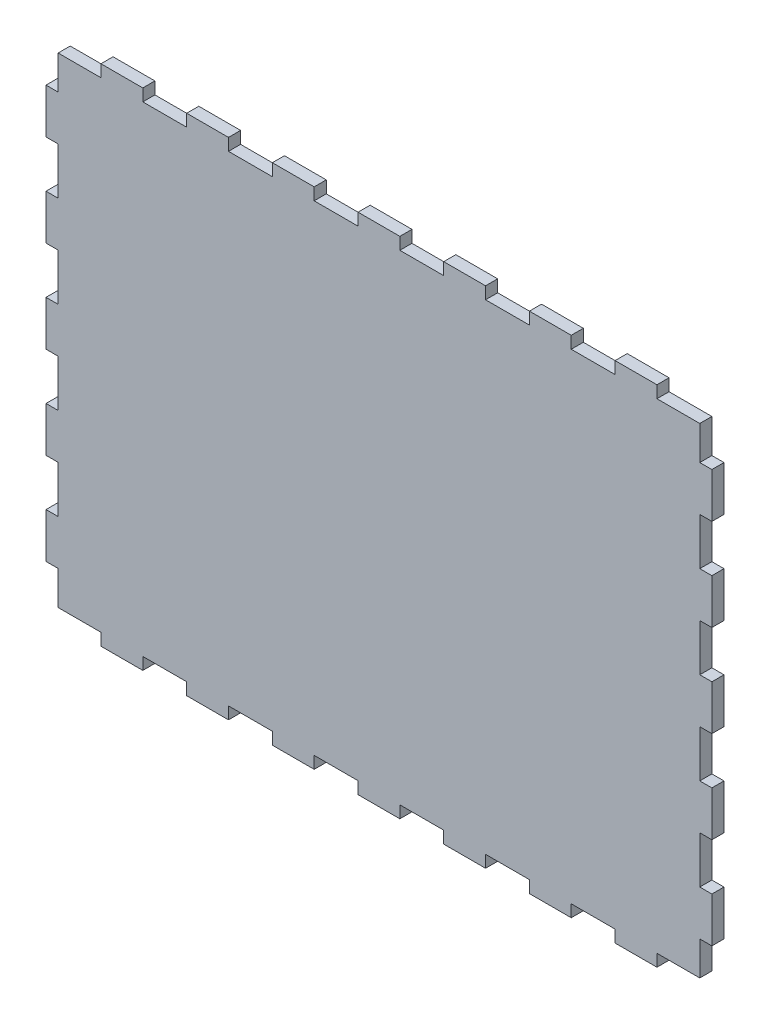
SolidWorks part; units mm, degrees
material "Plywood"
ref_plane "Front Plane" through (0, 0, 0) normal (0, 0, 1) x (1, 0, 0)
ref_plane "Top Plane" through (0, 0, 0) normal (0, 1, 0) x (1, 0, 0)
ref_plane "Right Plane" through (0, 0, 0) normal (1, 0, 0) x (0, 0, -1)
ref_plane "Plane1" through (0, 0, 6) normal (0, 0, 1) x (1, 0, 0)
sketch "Sketch1" plane through (0, 0, 6) normal (0, 0, 1) x (1, 0, 0)
  line L0 (302.7667, 244) -> (302.7667, 250)
  line L1 (302.7667, 250) -> (282.0333, 250)
  line L2 (282.0333, 250) -> (282.0333, 244)
  line L3 (282.0333, 244) -> (260.3, 244)
  line L4 (260.3, 244) -> (260.3, 250)
  line L5 (260.3, 250) -> (239.5667, 250)
  line L6 (239.5667, 250) -> (239.5667, 244)
  line L7 (239.5667, 244) -> (217.8333, 244)
  line L8 (217.8333, 244) -> (217.8333, 250)
  line L9 (217.8333, 250) -> (197.1, 250)
  line L10 (197.1, 250) -> (197.1, 244)
  line L11 (197.1, 244) -> (175.3667, 244)
  line L12 (175.3667, 244) -> (175.3667, 250)
  line L13 (175.3667, 250) -> (154.6333, 250)
  line L14 (154.6333, 250) -> (154.6333, 244)
  line L15 (154.6333, 244) -> (132.9, 244)
  line L16 (132.9, 244) -> (132.9, 250)
  line L17 (132.9, 250) -> (112.1667, 250)
  line L18 (112.1667, 250) -> (112.1667, 244)
  line L19 (112.1667, 244) -> (90.4333, 244)
  line L20 (90.4333, 244) -> (90.4333, 250)
  line L21 (90.4333, 250) -> (69.7, 250)
  line L22 (69.7, 250) -> (69.7, 244)
  line L23 (69.7, 244) -> (47.9667, 244)
  line L24 (47.9667, 244) -> (47.9667, 250)
  line L25 (47.9667, 250) -> (27.2333, 250)
  line L26 (27.2333, 250) -> (27.2333, 244)
  line L27 (27.2333, 244) -> (6, 244)
  line L28 (6, 244) -> (6, 227.2273)
  line L29 (6, 227.2273) -> (0, 227.2273)
  line L30 (0, 227.2273) -> (0, 204.9545)
  line L31 (0, 204.9545) -> (6, 204.9545)
  line L32 (6, 204.9545) -> (6, 181.6818)
  line L33 (6, 181.6818) -> (0, 181.6818)
  line L34 (0, 181.6818) -> (0, 159.4091)
  line L35 (0, 159.4091) -> (6, 159.4091)
  line L36 (6, 159.4091) -> (6, 136.1364)
  line L37 (6, 136.1364) -> (0, 136.1364)
  line L38 (0, 136.1364) -> (0, 113.8636)
  line L39 (0, 113.8636) -> (6, 113.8636)
  line L40 (6, 113.8636) -> (6, 90.5909)
  line L41 (6, 90.5909) -> (0, 90.5909)
  line L42 (0, 90.5909) -> (0, 68.3182)
  line L43 (0, 68.3182) -> (6, 68.3182)
  line L44 (6, 68.3182) -> (6, 45.0455)
  line L45 (6, 45.0455) -> (0, 45.0455)
  line L46 (0, 45.0455) -> (0, 22.7727)
  line L47 (0, 22.7727) -> (6, 22.7727)
  line L48 (6, 22.7727) -> (6, 6)
  line L49 (6, 6) -> (27.2333, 6)
  line L50 (27.2333, 6) -> (27.2333, 0)
  line L51 (27.2333, 0) -> (47.9667, 0)
  line L52 (47.9667, 0) -> (47.9667, 6)
  line L53 (47.9667, 6) -> (69.7, 6)
  line L54 (69.7, 6) -> (69.7, 0)
  line L55 (69.7, 0) -> (90.4333, 0)
  line L56 (90.4333, 0) -> (90.4333, 6)
  line L57 (90.4333, 6) -> (112.1667, 6)
  line L58 (112.1667, 6) -> (112.1667, 0)
  line L59 (112.1667, 0) -> (132.9, 0)
  line L60 (132.9, 0) -> (132.9, 6)
  line L61 (132.9, 6) -> (154.6333, 6)
  line L62 (154.6333, 6) -> (154.6333, 0)
  line L63 (154.6333, 0) -> (175.3667, 0)
  line L64 (175.3667, 0) -> (175.3667, 6)
  line L65 (175.3667, 6) -> (197.1, 6)
  line L66 (197.1, 6) -> (197.1, 0)
  line L67 (197.1, 0) -> (217.8333, 0)
  line L68 (217.8333, 0) -> (217.8333, 6)
  line L69 (217.8333, 6) -> (239.5667, 6)
  line L70 (239.5667, 6) -> (239.5667, 0)
  line L71 (239.5667, 0) -> (260.3, 0)
  line L72 (260.3, 0) -> (260.3, 6)
  line L73 (260.3, 6) -> (282.0333, 6)
  line L74 (282.0333, 6) -> (282.0333, 0)
  line L75 (282.0333, 0) -> (302.7667, 0)
  line L76 (302.7667, 0) -> (302.7667, 6)
  line L77 (302.7667, 6) -> (324, 6)
  line L78 (324, 6) -> (324, 22.7727)
  line L79 (324, 22.7727) -> (330, 22.7727)
  line L80 (330, 22.7727) -> (330, 45.0455)
  line L81 (330, 45.0455) -> (324, 45.0455)
  line L82 (324, 45.0455) -> (324, 68.3182)
  line L83 (324, 68.3182) -> (330, 68.3182)
  line L84 (330, 68.3182) -> (330, 90.5909)
  line L85 (330, 90.5909) -> (324, 90.5909)
  line L86 (324, 90.5909) -> (324, 113.8636)
  line L87 (324, 113.8636) -> (330, 113.8636)
  line L88 (330, 113.8636) -> (330, 136.1364)
  line L89 (330, 136.1364) -> (324, 136.1364)
  line L90 (324, 136.1364) -> (324, 159.4091)
  line L91 (324, 159.4091) -> (330, 159.4091)
  line L92 (330, 159.4091) -> (330, 181.6818)
  line L93 (330, 181.6818) -> (324, 181.6818)
  line L94 (324, 181.6818) -> (324, 204.9545)
  line L95 (324, 204.9545) -> (330, 204.9545)
  line L96 (330, 204.9545) -> (330, 227.2273)
  line L97 (330, 227.2273) -> (324, 227.2273)
  line L98 (324, 227.2273) -> (324, 244)
  line L99 (324, 244) -> (302.7667, 244)
extrude "Boss-Extrude1" add sketch "Sketch1" against normal blind 6
